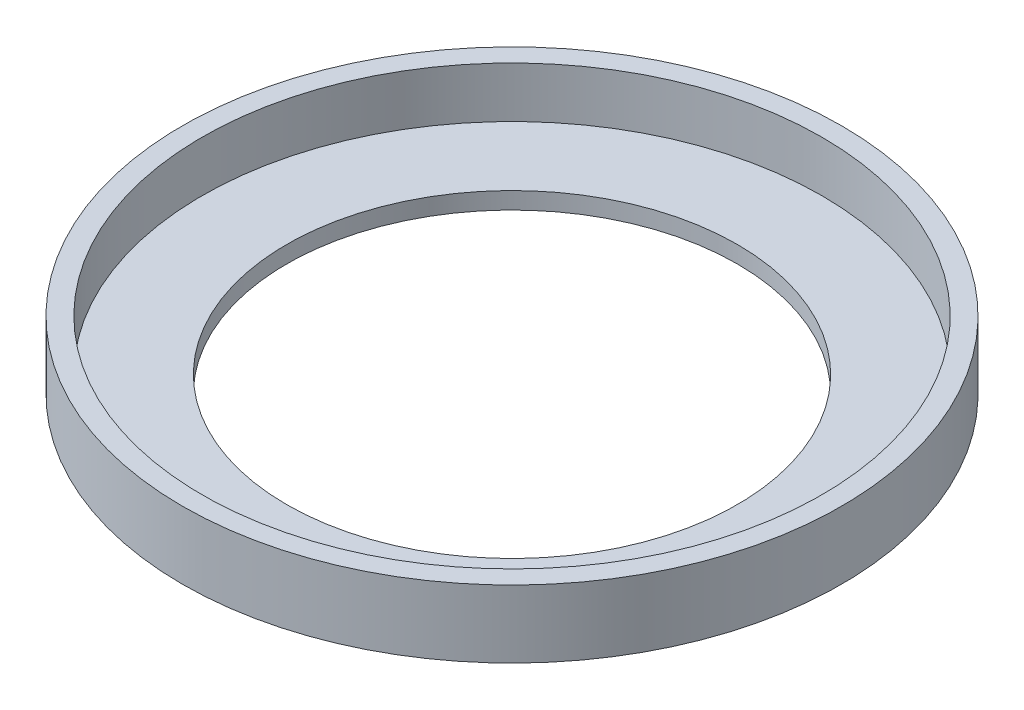
SolidWorks part; units mm, degrees
ref_plane "Спереди" through (0, 0, 0) normal (0, 0, 1) x (1, 0, 0)
ref_plane "Сверху" through (0, 0, 0) normal (0, 1, 0) x (1, 0, 0)
ref_plane "Справа" through (0, 0, 0) normal (1, 0, 0) x (0, 0, -1)
sketch "Эскиз1" plane through (0, 0, 0) normal (0, 0, 1) x (1, 0, 0)
  line L0 (0, 0) -> (0, 23.2211) construction
  line L1 (4, 0) -> (5.85, 0)
  line L2 (5.85, 0) -> (5.85, 1.2)
  line L3 (5.85, 1.2) -> (5.5, 1.2)
  line L4 (5.5, 1.2) -> (5.5, 0.3)
  line L5 (5.5, 0.3) -> (4, 0.3)
  line L6 (4, 0.3) -> (4, 0)
  dimension "D1" = 8
  dimension "D2" = 11.7
  dimension "D3" = 0.3
  dimension "D4" = 1.2
  dimension "D5" = 11
revolve "Повернуть1" add sketch "Эскиз1" angle 360 about L0
